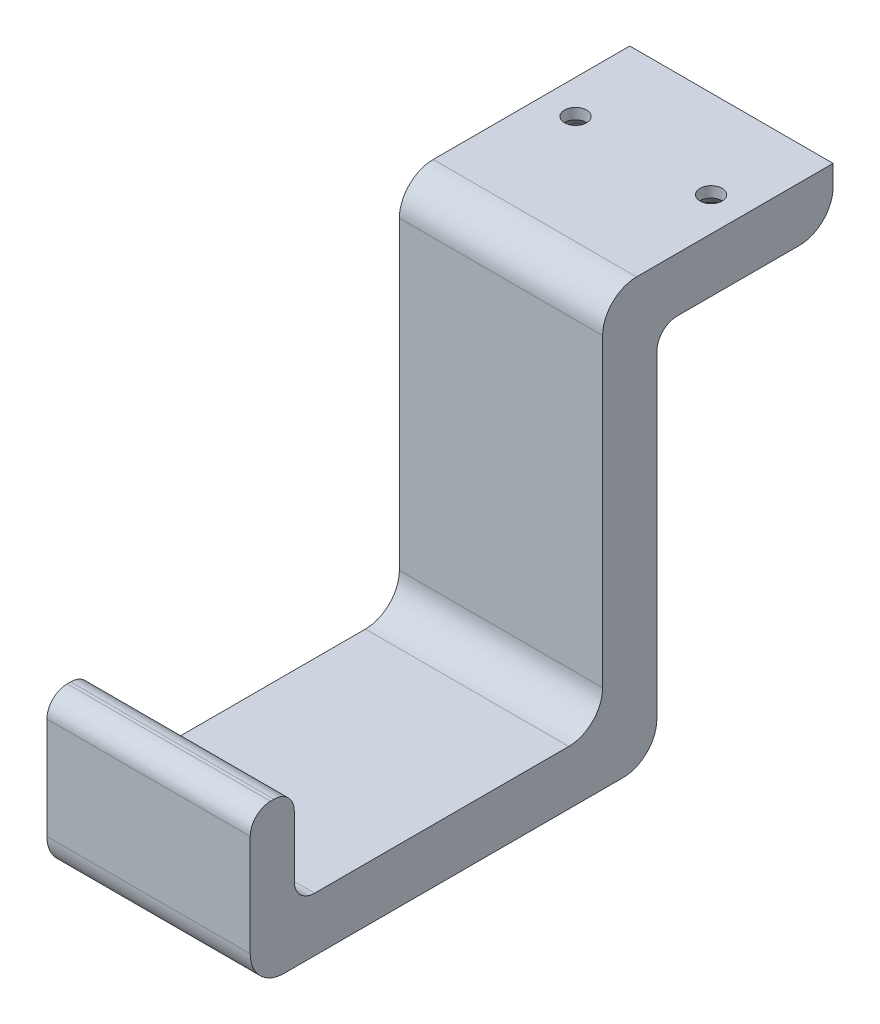
SolidWorks part; units mm, degrees
material "PLA Polyacetic Acid"
ref_plane "Front Plane" through (0, 0, 0) normal (0, 0, 1) x (1, 0, 0)
ref_plane "Top Plane" through (0, 0, 0) normal (0, 1, 0) x (1, 0, 0)
ref_plane "Right Plane" through (0, 0, 0) normal (1, 0, 0) x (0, 0, -1)
sketch "Sketch1" plane through (0, 0, 0) normal (1, 0, 0) x (0, 0, -1)
  line L0 (-60, 0) -> (0, 0)
  line L1 (0, 0) -> (0, 55)
  line L2 (0, 55) -> (26, 55)
  line L3 (-60, 0) -> (-60, 23)
  line L4 (-60, 23) -> (-53.5, 23)
  line L5 (-53.5, 23) -> (-53.5, 8)
  line L6 (-53.5, 8) -> (-8, 8)
  line L7 (-8, 8) -> (-8, 63)
  line L8 (-8, 63) -> (26, 63)
  line L9 (26, 63) -> (26, 55)
  line L10 (-8, 55) -> (0, 55) construction
  line L11 (0, 63) -> (0, 55) construction
  line L12 (-8, 8) -> (-8, 0) construction
  dimension "D1" = 60
  dimension "D2" = 63
  dimension "D3" = 26
  dimension "D4" = 15
  dimension "D5" = 6.5
  dimension "D6" = 8
  dimension "D7" = 34
  dimension "D8" = 45.5
extrude "Boss-Extrude1" add sketch "Sketch1" along normal mid plane 30
fillet "Fillet1" radius 5 5 edges at (0, 8, 8) (0, 63, 8) (0, 0, 0) (0, 0, 60) (0, 55, -26)
fillet "Fillet2" radius 3 4 edges at (0, 23, 53.5) (0, 23, 60) (0, 8, 53.5) (0, 55, 0)
hole_wizard "CSK for #4 Flat Head Machine Screw2" positions "Sketch5" profile "Sketch6" countersink size "#4" standard "ANSI Inch" end condition up to next
sketch "Sketch5" plane through (0, 55, 0) normal (0, -1, 0) x (1, 0, 0)
  line L0 (0, 0) -> (0, -26) construction
  line L1 (15, 0) -> (-15, 0) construction
  line L2 (15, -26) -> (-15, -26) construction
  line L5 (0, -13) -> (-10, -13) construction
  point P0 (-10, -13)
  point P15 (10, -13)
  dimension "D1" = 20
sketch "Sketch6" plane through (-10, 55, -13) normal (1, 0, 0) x (0, 0, -1)
  line L0 (0, 0) -> (0, 8)
  line L1 (0, 8) -> (1.6319, 8)
  line L2 (1.6319, 8) -> (1.6319, 6.4098)
  line L3 (1.6319, 6.4098) -> (2.8575, 5)
  line L4 (2.8575, 5) -> (2.8575, 0)
  line L6 (2.8575, 0) -> (0, 0)
  line L7 (-1.632, 6.4098) -> (-2.8575, 5) construction
  line L11 (0, -6.35) -> (0, 107.95) construction
  dimension "Thru Hole Dia." = 3.2639
  dimension "Thru Hole Depth" = 8
  dimension "C'Sink Dia." = 5.715
  dimension "C'Sink Angle" = 82
  dimension "Head Clearance" = 5
